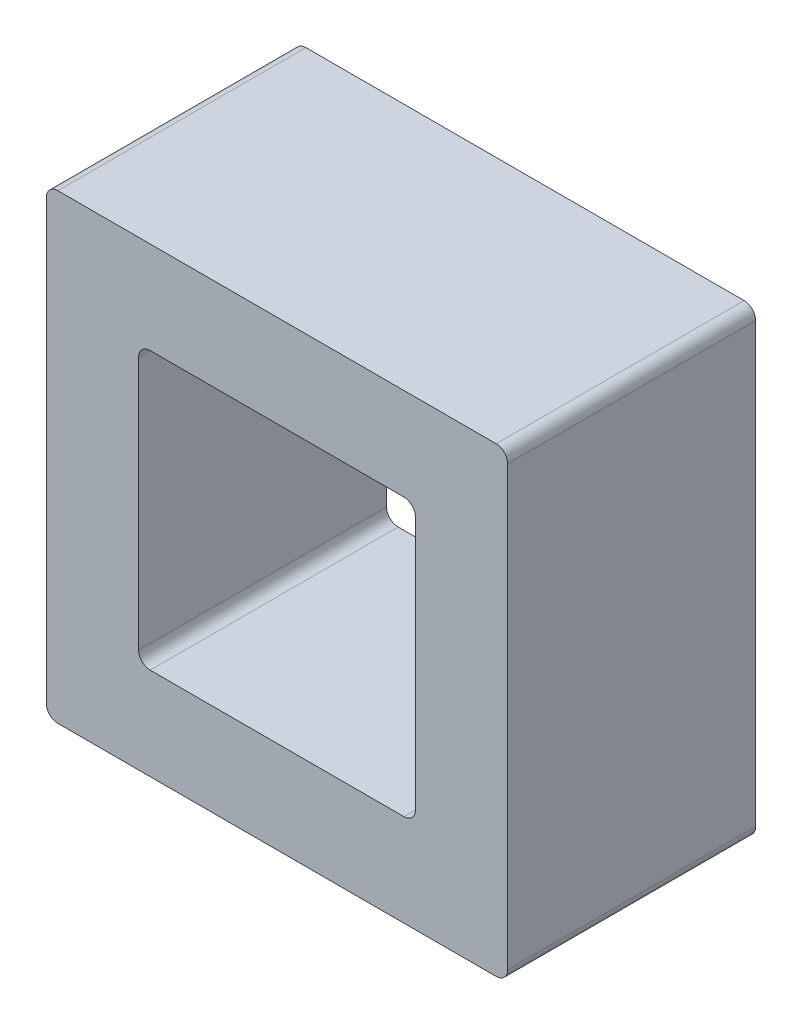
SolidWorks part; units mm, degrees
ref_plane "Front Plane" through (0, 0, 0) normal (0, 0, 1) x (1, 0, 0)
ref_plane "Top Plane" through (0, 0, 0) normal (0, 1, 0) x (1, 0, 0)
ref_plane "Right Plane" through (0, 0, 0) normal (1, 0, 0) x (0, 0, -1)
sketch "Sketch1" plane through (0, 0, 0) normal (0, 0, 1) x (1, 0, 0)
  line L1 (0, 0) -> (8, 0)
  line L2 (0, 0) -> (0, 8)
  line L3 (0, 8) -> (8, 8)
  line L4 (8, 0) -> (8, 8)
  line L5 (1.6, 6.4) -> (6.4, 6.4)
  line L6 (1.6, 6.4) -> (1.6, 1.6)
  line L7 (1.6, 1.6) -> (6.4, 1.6)
  line L8 (6.4, 6.4) -> (6.4, 1.6)
  point P9 (4, 8)
  point P10 (4, 6.4)
  point P11 (6.4, 4)
  point P12 (8, 4)
  dimension "D1" = 8
  dimension "D2" = 8
  dimension "D3" = 1.6
  dimension "D4" = 1.6
extrude "Boss-Extrude1" add sketch "Sketch1" along normal blind 4.3
fillet "Fillet1" radius 0.2 8 edges at (8, 0, 2.15) (0, 0, 2.15) (8, 8, 2.15) (0, 8, 2.15) (6.4, 1.6, 2.15) (6.4, 6.4, 2.15) (1.6, 1.6, 2.15) (1.6, 6.4, 2.15)
